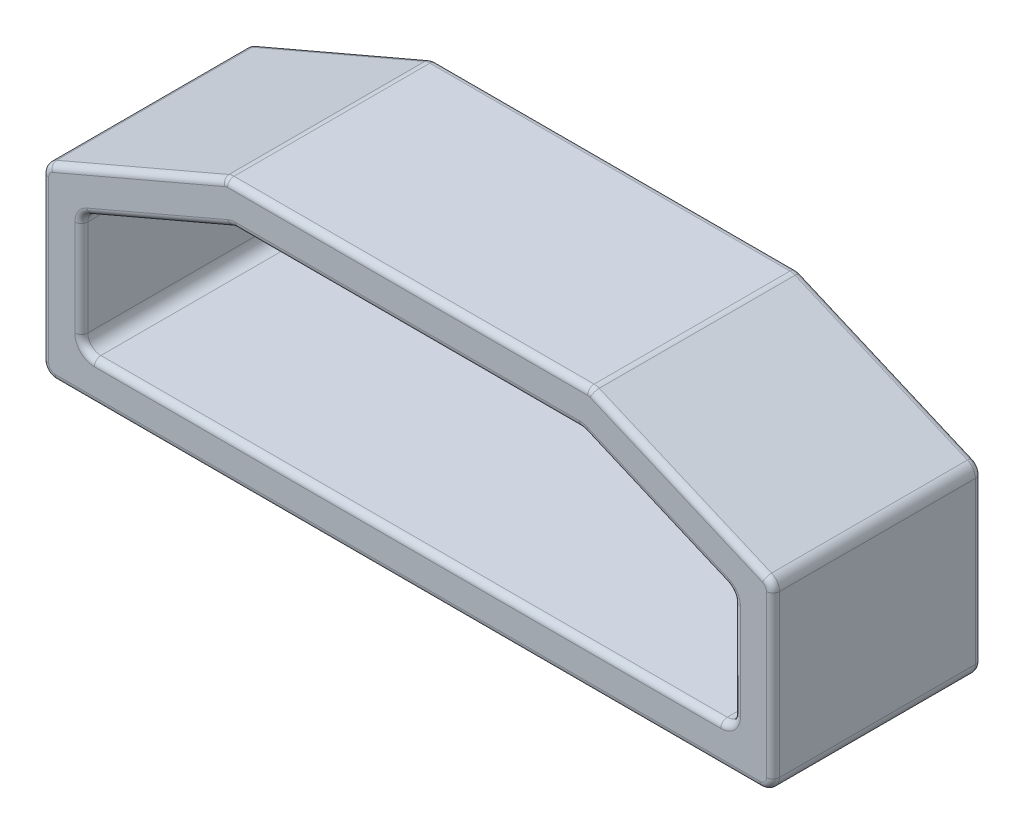
SolidWorks part; units mm, degrees
ref_plane "Front Plane" through (0, 0, 0) normal (0, 0, 1) x (1, 0, 0)
ref_plane "Top Plane" through (0, 0, 0) normal (0, 1, 0) x (1, 0, 0)
ref_plane "Right Plane" through (0, 0, 0) normal (1, 0, 0) x (0, 0, -1)
sketch "Sketch1" plane through (0, 0, 0) normal (0, 0, 1) x (1, 0, 0)
  line L0 (0, 0) -> (0, 62.0609) construction
  line L1 (14, 0) -> (-14, 0)
  line L2 (-14, 0) -> (-14, 7)
  line L3 (14, 0) -> (14, 7)
  line L4 (-14, 7) -> (-7, 10)
  line L5 (14, 7) -> (7, 10)
  line L6 (-7, 10) -> (7, 10)
  line L7 (12.5, 1.5) -> (-12.5, 1.5)
  line L8 (-12.5, 1.5) -> (-12.5, 6.0109)
  line L9 (-12.5, 6.0109) -> (-6.6921, 8.5)
  line L10 (-6.6921, 8.5) -> (6.6921, 8.5)
  line L11 (12.5, 6.0109) -> (6.6921, 8.5)
  line L12 (12.5, 1.5) -> (12.5, 6.0109)
  point P9 (0, 10)
  dimension "D1" = 10
  dimension "D2" = 28
  dimension "D3" = 14
  dimension "D4" = 7
  dimension "D5" = 1.5
extrude "Boss-Extrude1" add sketch "Sketch1" along normal blind 8
fillet "Fillet1" radius 0.5 12 edges at (12.5, 1.5, 4) (12.5, 6.0109, 4) (6.6921, 8.5, 4) (-6.6921, 8.5, 4) (-12.5, 6.0109, 4) (-12.5, 1.5, 4) (14, 7, 4) (14, 0, 4) (-14, 0, 4) (-14, 7, 4) (-7, 10, 4) (7, 10, 4)
fillet "Fillet2" radius 0.25 48 edges at (-12.4174, 5.9565, 0) (-9.4917, 7.3002, 0) (-6.69, 8.4898, 0) (0, 8.5, 0) (6.69, 8.4898, 0) (9.4917, 7.3002, 0) (12.4174, 5.9565, 0) (12.5, 3.8406, 0) (12.3536, 1.6464, 0) (0, 1.5, 0) (-12.3536, 1.6464, 0) (-12.5, 3.8406, 0) (6.9979, 9.9898, 0) (0, 10, 0) (-6.9979, 9.9898, 0) (-10.3956, 8.5447, 0) (-13.9174, 6.9455, 0) (-14, 3.5852, 0) (-13.8536, 0.1464, 0) (0, 0, 0) (13.8536, 0.1464, 0) (14, 3.5852, 0) (13.9174, 6.9455, 0) (10.3956, 8.5447, 0) (12.4174, 5.9565, 8) (9.4917, 7.3002, 8) (6.69, 8.4898, 8) (0, 8.5, 8) (-6.69, 8.4898, 8) (-9.4917, 7.3002, 8) (-12.4174, 5.9565, 8) (-12.5, 3.8406, 8) (-12.3536, 1.6464, 8) (0, 1.5, 8) (12.3536, 1.6464, 8) (12.5, 3.8406, 8) (13.8536, 0.1464, 8) (0, 0, 8) (-13.8536, 0.1464, 8) (-14, 3.5852, 8) (-13.9174, 6.9455, 8) (-10.3956, 8.5447, 8) (-6.9979, 9.9898, 8) (0, 10, 8) (6.9979, 9.9898, 8) (10.3956, 8.5447, 8) (13.9174, 6.9455, 8) (14, 3.5852, 8)
